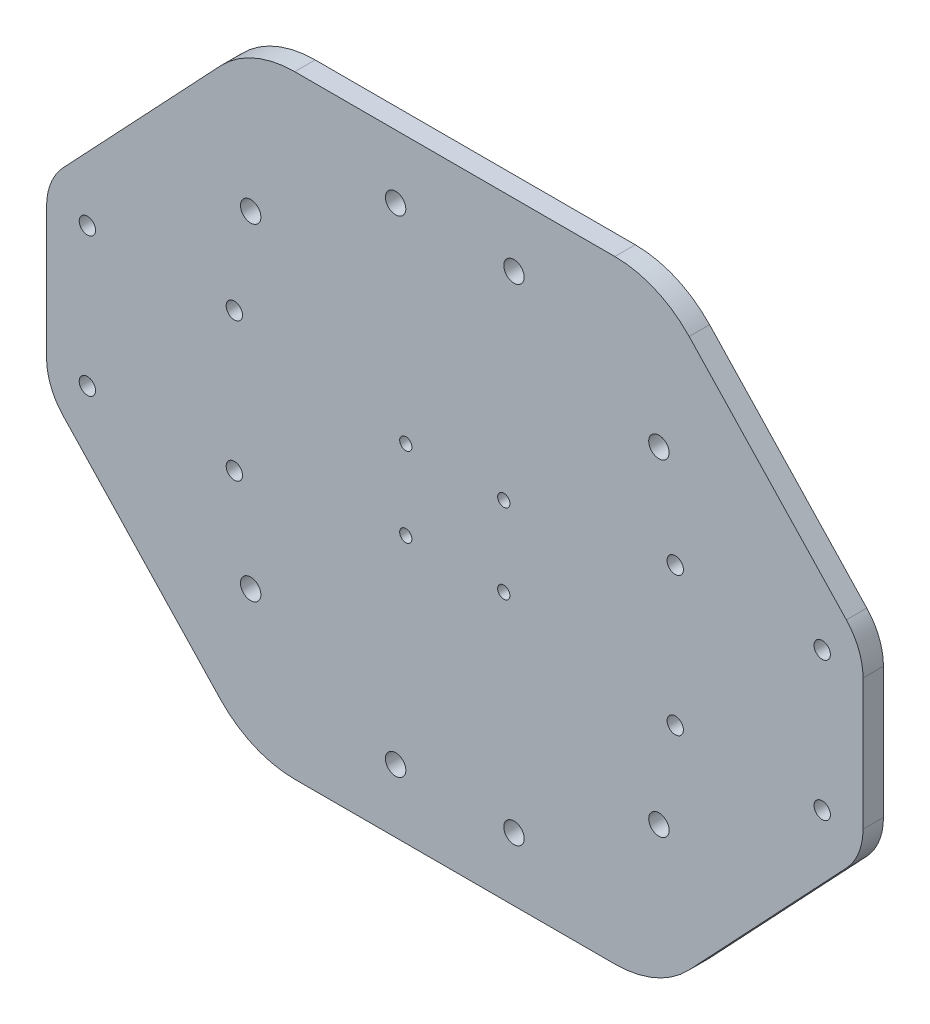
SolidWorks part; units mm, degrees
ref_plane "Alzado" through (0, 0, 0) normal (0, 0, 1) x (1, 0, 0)
ref_plane "Planta" through (0, 0, 0) normal (0, 1, 0) x (1, 0, 0)
ref_plane "Vista lateral" through (0, 0, 0) normal (1, 0, 0) x (0, 0, -1)
sketch "Croquis1" plane through (0, 0, 0) normal (0, 0, 1) x (1, 0, 0)
  line L0 (200, 5.6488) -> (0, 5.6488) construction
  line L1 (200, -69.4012) -> (0, -69.4012)
  line L2 (200, -69.4012) -> (200, 80.6988)
  line L3 (200, 80.6988) -> (0, 80.6988)
  line L4 (0, -69.4012) -> (0, 80.6988)
  line L5 (100, 80.6988) -> (100, -69.4012) construction
  line L6 (70, 80.6988) -> (70, 49.6988) construction
  line L7 (70, 49.6988) -> (130, 49.6988) construction
  line L8 (130, 49.6988) -> (130, 80.6988) construction
  circle A0 centre (150, 45.6988) radius 12 construction
  circle A1 centre (50, 45.6988) radius 12 construction
  circle A2 centre (85.5, 65.1988) radius 2.5
  circle A3 centre (114.5, 65.1988) radius 2.5
  circle A4 centre (50, 45.6988) radius 2.5
  circle A5 centre (150, 45.6988) radius 2.5
  circle A6 centre (150, -34.4012) radius 2.5
  circle A7 centre (150, -34.4012) radius 12 construction
  circle A8 centre (114.5, -53.9012) radius 2.5
  circle A9 centre (85.5, -53.9012) radius 2.5
  circle A10 centre (50, -34.4012) radius 2.5
  circle A11 centre (50, -34.4012) radius 12 construction
  point P14 (100, 49.6988)
  point P24 (70, 65.1988)
  point P26 (130, 65.1988)
  dimension "D5" = 15.5
  dimension "D7" = 5
  dimension "D8" = 5
  dimension "D9" = 5
  dimension "D10" = 5
  dimension "D1" = 31
  dimension "D2" = 60
  dimension "D3" = 40.05
  dimension "D4" = 20
  dimension "D6" = 15.5
extrude "Saliente-Extruir1" add sketch "Croquis1" along normal blind 5
sketch "Croquis2" plane through (0, 0, 5) normal (0, 0, 1) x (1, 0, 0)
  line L0 (200, 5.6488) -> (0, 5.6488) construction
  line L1 (200, -69.4012) -> (200, 80.6988) construction
  line L2 (0, 80.6988) -> (0, -69.4012) construction
  line L3 (100, 80.6988) -> (100, -69.4012) construction
  line L4 (200, 80.6988) -> (0, 80.6988) construction
  line L5 (0, -69.4012) -> (200, -69.4012) construction
  line L6 (28, -11.3512) -> (28, 22.6488) construction
  line L7 (88, -4.1012) -> (112, -4.1012) construction
  line L8 (88, -4.1012) -> (88, 15.3988) construction
  line L9 (88, 15.3988) -> (112, 15.3988) construction
  line L10 (112, -4.1012) -> (112, 15.3988) construction
  line L11 (88, -4.1012) -> (112, 15.3988) construction
  line L12 (88, 15.3988) -> (112, -4.1012) construction
  line L13 (10, -11.3512) -> (46, -11.3512) construction
  line L14 (10, -11.3512) -> (10, 22.6488) construction
  line L15 (10, 22.6488) -> (46, 22.6488) construction
  line L16 (46, -11.3512) -> (46, 22.6488) construction
  line L17 (10, -11.3512) -> (46, 22.6488) construction
  line L18 (10, 22.6488) -> (46, -11.3512) construction
  circle A0 centre (88, 15.3988) radius 1.5
  circle A1 centre (112, 15.3988) radius 1.5
  circle A2 centre (88, -4.1012) radius 1.5
  circle A3 centre (112, -4.1012) radius 1.5
  circle A4 centre (10, 22.6488) radius 2
  circle A5 centre (46, 22.6488) radius 2
  circle A6 centre (46, -11.3512) radius 2
  circle A7 centre (10, -11.3512) radius 2
  circle A8 centre (190, -11.3512) radius 2
  circle A9 centre (154, -11.3512) radius 2
  circle A10 centre (154, 22.6488) radius 2
  circle A11 centre (190, 22.6488) radius 2
  point P12 (100, 5.6488)
  point P22 (28, 5.6488)
  dimension "D3" = 3
  dimension "D7" = 4
  dimension "D1" = 24
  dimension "D2" = 19.5
  dimension "D4" = 36
  dimension "D5" = 34
  dimension "D6" = 10
extrude "Cortar-Extruir1" cut sketch "Croquis2" against normal blind 10
sketch "Croquis3" plane through (0, 0, 0) normal (0, 0, -1) x (-1, 0, 0)
  line L0 (-200, 5.6488) -> (0, 5.6488) construction
  line L1 (-200, -69.4012) -> (-200, 80.6988) construction
  line L2 (0, 80.6988) -> (0, -69.4012) construction
  line L3 (-100, 80.6988) -> (-100, -69.4012) construction
  line L4 (-200, 80.6988) -> (0, 80.6988) construction
  line L5 (0, -69.4012) -> (-200, -69.4012) construction
  line L6 (-157.4016, 72.8458) -> (-195.9157, 31.9822)
  line L11 (-200, -69.4012) -> (0, 80.6988) construction
  line L12 (-200, 80.6988) -> (0, -69.4012) construction
  line L13 (-42.5984, 72.8458) -> (-4.0843, 31.9822)
  line L14 (-42.5984, -61.5481) -> (-4.0843, -20.6845)
  line L15 (-157.4016, -61.5481) -> (-195.9157, -20.6845)
  line L16 (-60.7914, 80.6988) -> (0, 80.6988)
  line L17 (-200, 80.6988) -> (-139.2086, 80.6988)
  line L18 (-200, 80.6988) -> (-200, 21.6941)
  line L19 (-200, -69.4012) -> (0, -69.4012)
  line L20 (-139.2086, -69.4012) -> (-60.7914, -69.4012) construction
  line L24 (0, 80.6988) -> (0, 21.6941)
  line L25 (-200, 80.6988) -> (0, -69.4012) construction
  line L26 (-200, -69.4012) -> (0, 80.6988) construction
  line L27 (-200, -10.3964) -> (-200, -69.4012)
  line L28 (0, -10.3964) -> (0, -69.4012)
  line L29 (-200, 21.6941) -> (-200, -10.3964) construction
  line L30 (-139.2086, 80.6988) -> (-60.7914, 80.6988) construction
  line L31 (0, 21.6941) -> (0, -10.3964) construction
  line L32 (-139.2086, -69.4012) -> (-60.7914, -69.4012) construction
  arc A0 (-195.9157, 31.9822) -> (-200, 21.6941) centre (-185, 21.6941) ccw
  arc A1 (-4.0843, 31.9822) -> (0, 21.6941) centre (-15, 21.6941) cw
  arc A2 (-4.0843, -20.6845) -> (0, -10.3964) centre (-15, -10.3964) ccw
  arc A3 (-195.9157, -20.6845) -> (-200, -10.3964) centre (-185, -10.3964) cw
  arc A4 (-42.5984, -61.5481) -> (-60.7914, -69.4012) centre (-60.7914, -44.4012) cw
  arc A5 (-157.4016, -61.5481) -> (-139.2086, -69.4012) centre (-139.2086, -44.4012) ccw
  arc A6 (-42.5984, 72.8458) -> (-60.7914, 80.6988) centre (-60.7914, 55.6988) ccw
  arc A7 (-157.4016, 72.8458) -> (-139.2086, 80.6988) centre (-139.2086, 55.6988) cw
  point P12 (-100, 5.6488)
  point P18 (-100, 5.6488)
  line M28 (-200, 80.6988) -> (-200, -69.4012)
  line M29 (-200, -69.4012) -> (0, -69.4012)
  line M30 (0, -69.4012) -> (0, 80.6988)
  line M31 (0, 80.6988) -> (-200, 80.6988)
  dimension "D3" = 15
  dimension "D4" = 25
extrude "Cortar-Extruir2" cut sketch "Croquis3" against normal blind 400 contours L6 A7 A0 M31 M28 | A6 L13 A1 M30 M31 | L14 A4 L19 A2 M30 | A5 L15 A3 M28 M29
